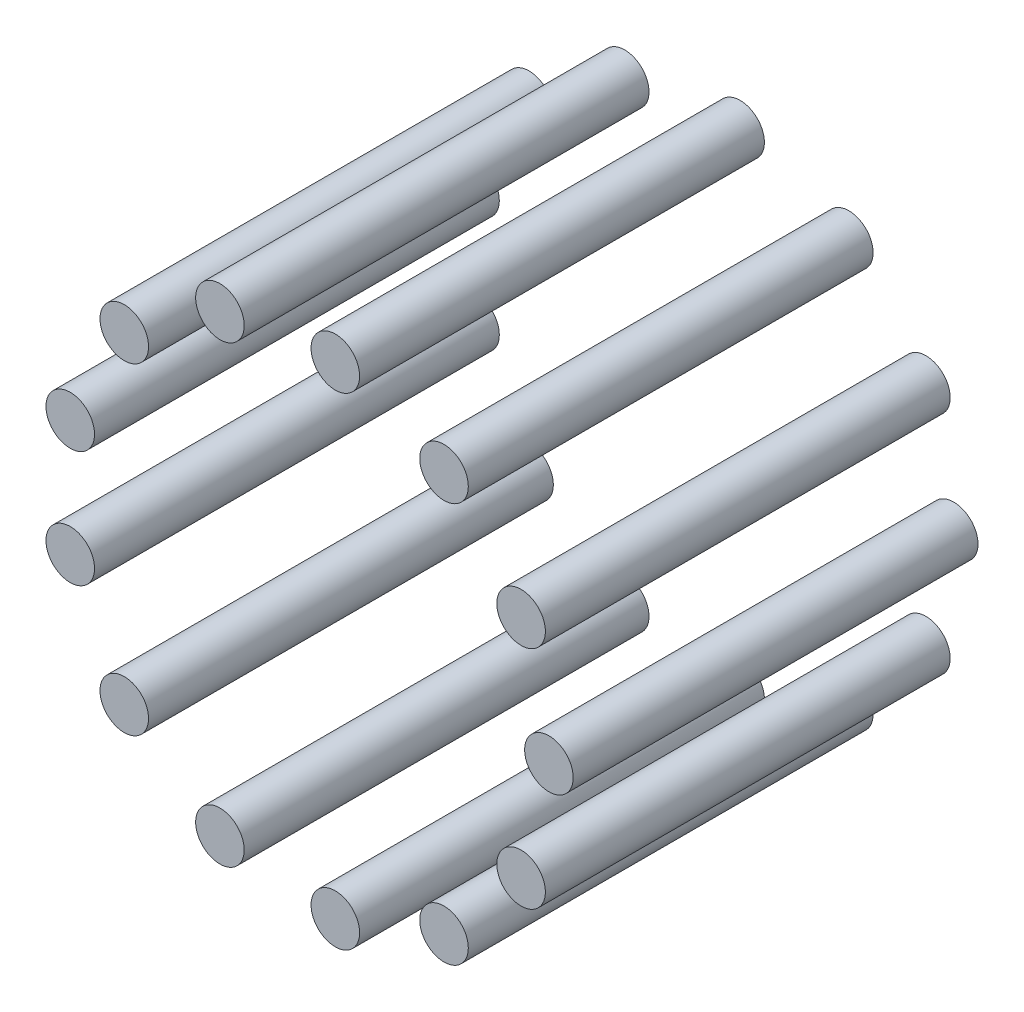
SolidWorks part; units mm, degrees
ref_plane "Front Plane" through (0, 0, 0) normal (0, 0, 1) x (1, 0, 0)
ref_plane "Top Plane" through (0, 0, 0) normal (0, 1, 0) x (1, 0, 0)
ref_plane "Right Plane" through (0, 0, 0) normal (1, 0, 0) x (0, 0, -1)
sketch "Sketch1" plane through (0, 0, 0) normal (0, 0, 1) x (1, 0, 0)
  line L0 (28.089, 0) -> (-28.8858, 0) construction
  line L1 (26.5637, 13.9417) -> (0, 0) construction
  circle A0 centre (0, 0) radius 30 construction
  circle A1 centre (30, 0) radius 3
  circle A2 centre (26.5637, -13.9417) radius 3
  circle A3 centre (17.0419, -24.6895) radius 3
  circle A4 centre (3.6161, -29.7813) radius 3
  circle A5 centre (-10.6381, -28.0505) radius 3
  circle A6 centre (-22.4553, -19.8937) radius 3
  circle A7 centre (-29.1283, -7.1795) radius 3
  circle A8 centre (-29.1283, 7.1795) radius 3
  circle A9 centre (-22.4553, 19.8937) radius 3
  circle A10 centre (-10.6381, 28.0505) radius 3
  circle A11 centre (3.6161, 29.7813) radius 3
  circle A12 centre (17.0419, 24.6895) radius 3
  circle A13 centre (26.5637, 13.9417) radius 3
  point P5 (14.2909, 7.5004)
  point P32 (0, 0)
  dimension "D1" = 6
  dimension "D3" = 60
  dimension "D4" = 27.692
  dimension "D2" = 13
extrude "Boss-Extrude1" add sketch "Sketch1" along normal blind 50
